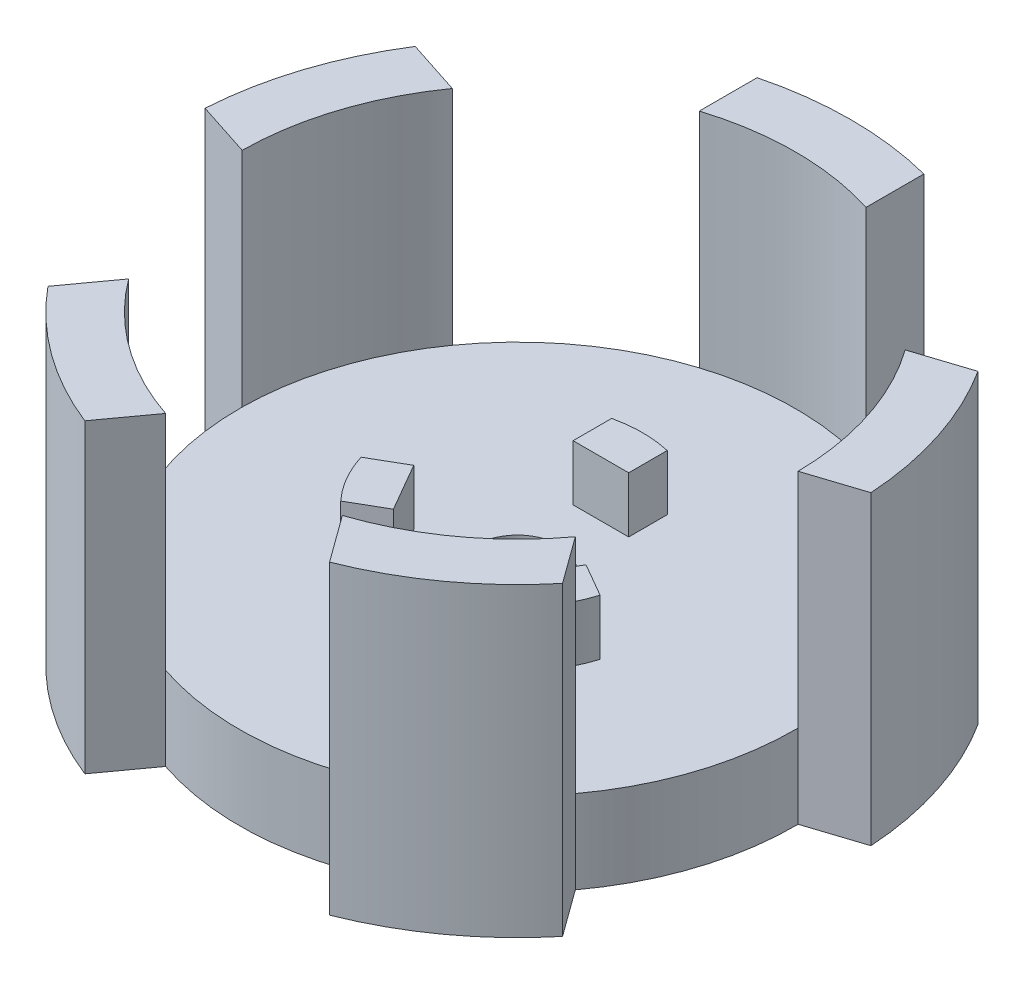
SolidWorks part; units mm, degrees
ref_plane "Front Plane" through (0, 0, 0) normal (0, 0, 1) x (1, 0, 0)
ref_plane "Top Plane" through (0, 0, 0) normal (0, 1, 0) x (1, 0, 0)
ref_plane "Right Plane" through (0, 0, 0) normal (1, 0, 0) x (0, 0, -1)
sketch "Sketch1" plane through (0, 0, 0) normal (0, 1, 0) x (1, 0, 0)
  circle A0 centre (0, 0) radius 10
  dimension "D1" = 20
extrude "Boss-Extrude1" add sketch "Sketch1" along normal blind 3
sketch "Sketch2" plane through (0, 3, 0) normal (0, 1, 0) x (1, 0, 0)
  line L1 (-1, 6) -> (1, 6)
  line L2 (-1, 6) -> (-1, 3)
  line L3 (-1, 3) -> (1, 3)
  line L4 (1, 6) -> (1, 3)
  line L5 (-1, 6) -> (1, 3) construction
  line L6 (-1, 3) -> (1, 6) construction
  point P0 (0, 4.5)
  dimension "D1" = 4.5
  dimension "D2" = 3
  dimension "D3" = 2
extrude "Boss-Extrude2" add sketch "Sketch2" along normal blind 2
pattern_circular "CirPattern1" count 3 over 360 about axis through (0, 0, 0) along (0, 1, 0) of "Boss-Extrude2"
sketch "Sketch3" plane through (0, 3, 0) normal (0, 1, 0) x (1, 0, 0)
  circle A0 centre (0, 0) radius 4.5
  circle A1 centre (0, 0) radius 9
  dimension "D1" = 9
extrude "Cut-Extrude1" cut sketch "Sketch3" along normal blind 2
sketch "Sketch4" plane through (0, 3, 0) normal (0, 1, 0) x (1, 0, 0)
  circle A0 centre (0, 0) radius 1.5
  dimension "D1" = 3
extrude "Cut-Extrude2" cut sketch "Sketch4" against normal blind 3
sketch "Sketch5" plane through (0, 3, 0) normal (0, 1, 0) x (1, 0, 0)
  line L1 (-3, 12) -> (3, 12)
  line L2 (-3, 12) -> (-3, 6)
  line L3 (-3, 6) -> (3, 6)
  line L4 (3, 12) -> (3, 6)
  line L5 (-3, 12) -> (3, 6) construction
  line L6 (-3, 6) -> (3, 12) construction
  circle A0 centre (0, 0) radius 9
  circle A1 centre (0, 0) radius 12
  point P3 (0, 9)
  circle M12 centre (0, 0) radius 10
  dimension "D1" = 18
  dimension "D2" = 6
  dimension "D3" = 6
extrude "Boss-Extrude3" add sketch "Sketch5" against normal blind 3 and the other way blind 8 contours L4 A1 L2 M12
pattern_circular "CirPattern2" count 5 over 360 about axis through (0, 0, 0) along (0, 1, 0) of "Boss-Extrude3"
